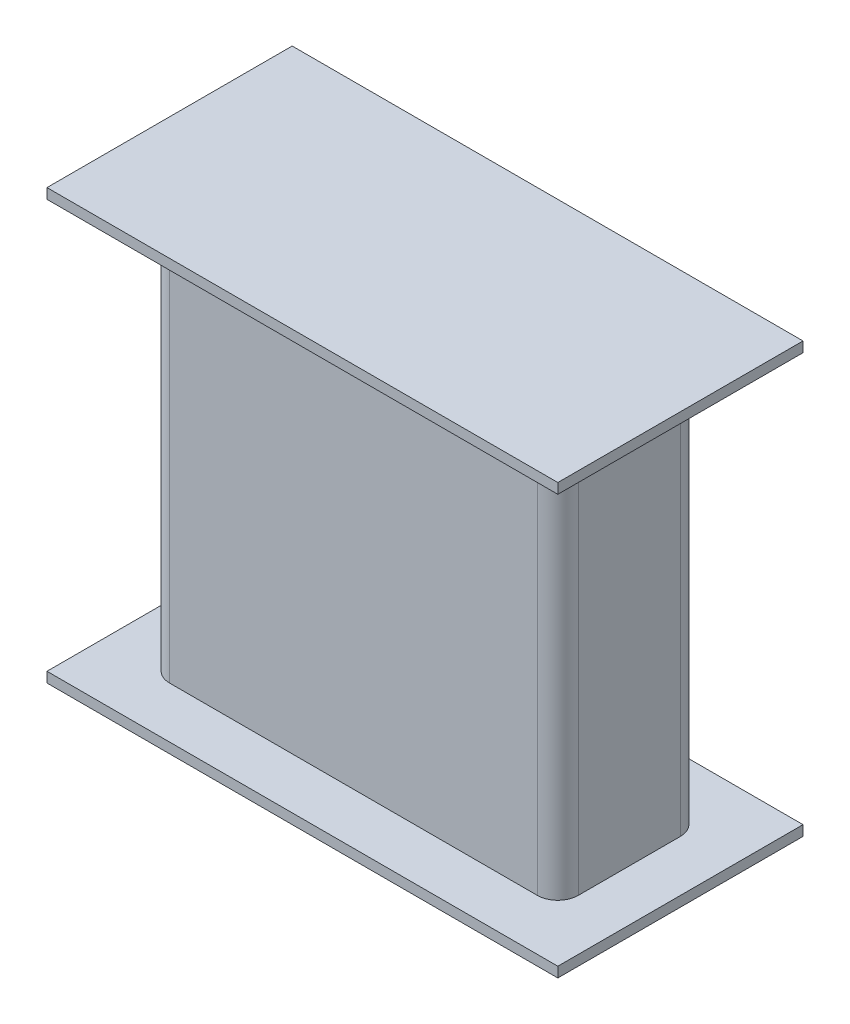
SolidWorks part; units mm, degrees
ref_plane "前视基准面" through (0, 0, 0) normal (0, 0, 1) x (1, 0, 0)
ref_plane "上视基准面" through (0, 0, 0) normal (0, 1, 0) x (1, 0, 0)
ref_plane "右视基准面" through (0, 0, 0) normal (1, 0, 0) x (0, 0, -1)
sketch "草图1" plane through (0, 0, 0) normal (0, 1, 0) x (1, 0, 0)
  line L1 (0, 14) -> (40, 14)
  line L2 (0, 14) -> (0, 0)
  line L3 (0, 0) -> (40, 0)
  line L4 (40, 14) -> (40, 0)
extrude "凸台-拉伸1" add sketch "草图1" along normal blind 40 contours L1 L4 L3 L2
sketch "草图6" plane through (0, 40, 0) normal (0, 1, 0) x (1, 0, 0)
  line L1 (2, 2) -> (38, 2)
  line L2 (2, 2) -> (2, 12)
  line L3 (2, 12) -> (38, 12)
  line L4 (38, 2) -> (38, 12)
extrude "切除-拉伸2" cut sketch "草图6" against normal through all contours L3 L4 L1 L2
sketch "草图15" plane through (0, 0, 0) normal (0, -1, 0) x (1, 0, 0)
  line L1 (2, -14) -> (38, -14)
  line L2 (0, -12) -> (0, -2)
  line L3 (2, 0) -> (38, 0)
  line L4 (40, -12) -> (40, -2)
  arc A0 (38, -14) -> (40, -12) centre (38, -12) ccw
  arc A1 (38, 0) -> (40, -2) centre (38, -2) cw
  arc A2 (2, -14) -> (0, -12) centre (2, -12) cw
  arc A3 (0, -2) -> (2, 0) centre (2, -2) cw
  point P10 (40, 0)
  point P13 (0, -14)
  dimension "D1" = 2
extrude "切除-拉伸5" cut sketch "草图15" against normal through all flip side to cut
sketch "草图16" plane through (0, 40, 0) normal (0, 1, 0) x (1, 0, 0)
  line L1 (-5, 19) -> (45, 19)
  line L2 (-5, 19) -> (-5, -5)
  line L3 (-5, -5) -> (45, -5)
  line L4 (45, 19) -> (45, -5)
extrude "凸台-拉伸2" add sketch "草图16" along normal blind 1
sketch "草图17" plane through (0, 0, 0) normal (0, -1, 0) x (1, 0, 0)
  line L1 (-5, -19) -> (45, -19)
  line L2 (-5, -19) -> (-5, 5)
  line L3 (-5, 5) -> (45, 5)
  line L4 (45, -19) -> (45, 5)
extrude "凸台-拉伸3" add sketch "草图17" along normal blind 1
sketch "草图18" plane through (0, -1, 0) normal (0, -1, 0) x (-1, 0, 0)
  line L1 (-2, 12) -> (-38, 12)
  line L2 (-2, 12) -> (-2, 2)
  line L3 (-2, 2) -> (-38, 2)
  line L4 (-38, 12) -> (-38, 2)
extrude "切除-拉伸6" cut sketch "草图18" against normal blind 1
ref_plane "基准面1" through (2, 40, -12) normal (0, 0, -1) x (-1, 0, 0)
